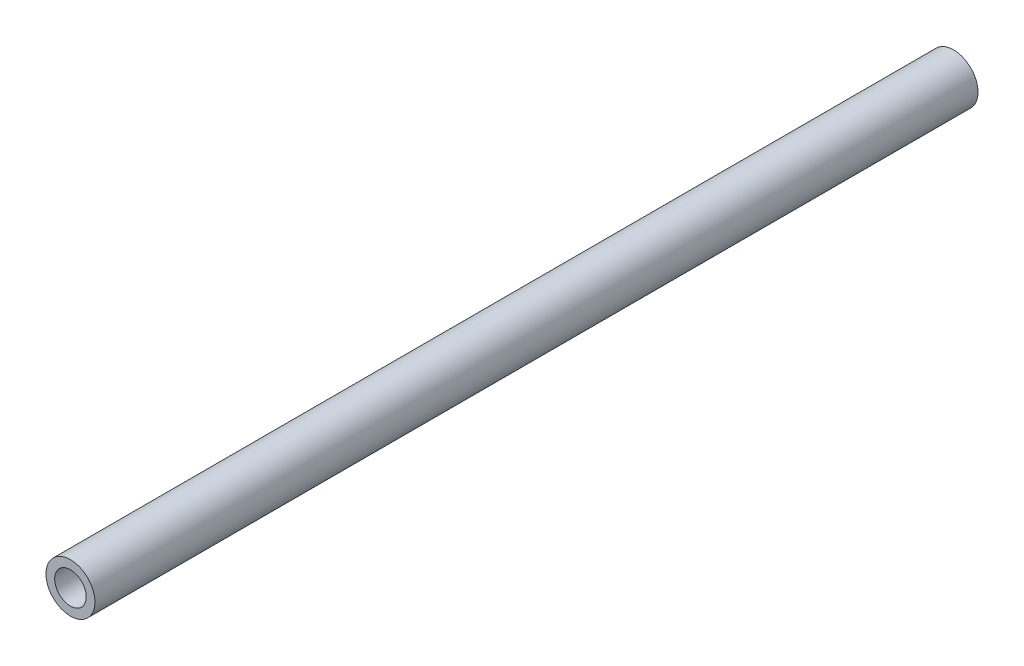
SolidWorks part; units mm, degrees
ref_plane "Front Plane" through (0, 0, 0) normal (0, 0, 1) x (1, 0, 0)
ref_plane "Top Plane" through (0, 0, 0) normal (0, 1, 0) x (1, 0, 0)
ref_plane "Right Plane" through (0, 0, 0) normal (1, 0, 0) x (0, 0, -1)
sketch "Sketch1" plane through (0, 0, 0) normal (0, 0, 1) x (1, 0, 0)
  circle A0 centre (0, 0) radius 0.97
  circle A1 centre (0, 0) radius 0.625
  dimension "D1" = 1.94
extrude "Boss-Extrude1" add sketch "Sketch1" along normal blind 35
